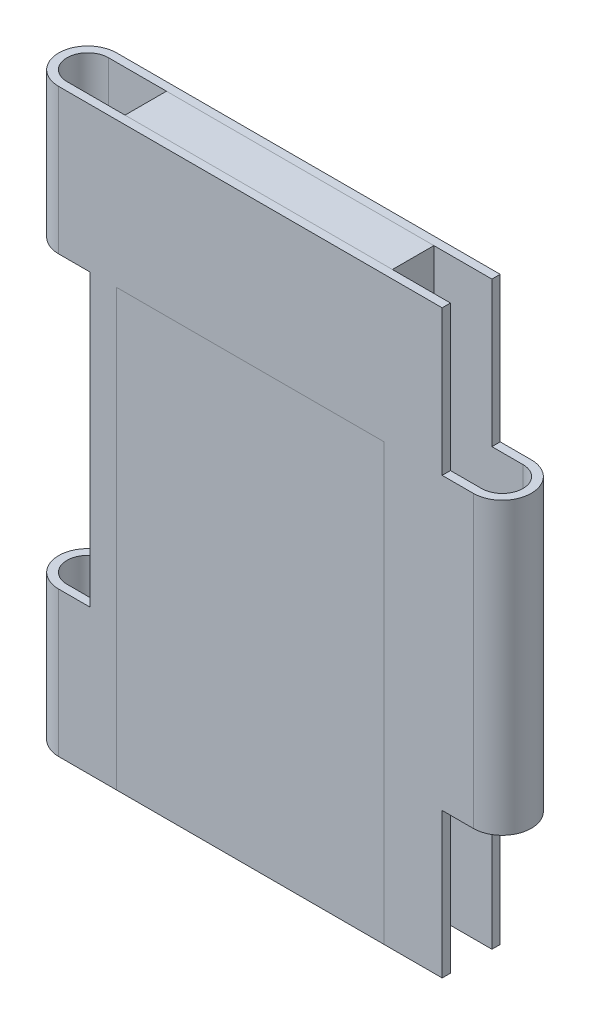
SolidWorks part; units mm, degrees
other "COLL.BOX-Boss-Extrude2"
ref_plane "Front Plane" through (0, 0, 0) normal (0, 0, 1) x (1, 0, 0)
ref_plane "Top Plane" through (0, 0, 0) normal (0, 1, 0) x (1, 0, 0)
ref_plane "Right Plane" through (0, 0, 0) normal (1, 0, 0) x (0, 0, -1)
sketch "Sketch1" plane through (0, 0, 0) normal (0, 1, 0) x (1, 0, 0)
  line L0 (-25, 0) -> (25, 0) construction
  line L1 (-25, 3.5) -> (25, 3.5)
  line L2 (-25, -3.5) -> (25, -3.5)
  line L3 (-25, 2.5) -> (25, 2.5)
  line L4 (-25, -2.5) -> (25, -2.5)
  arc A0 (-25, 3.5) -> (-25, -3.5) centre (-25, 0) ccw
  arc A1 (25, -3.5) -> (25, 3.5) centre (25, 0) ccw
  arc A2 (25, -2.5) -> (25, 2.5) centre (25, 0) ccw
  arc A3 (-25, 2.5) -> (-25, -2.5) centre (-25, 0) ccw
  point P2 (0, 0)
  dimension "D1" = 3.5
  dimension "50" = 50
  dimension "D2" = 1
extrude "Boss-Extrude1" add sketch "Sketch1" along normal blind 70
sketch "Sketch2" plane through (0, 0, 3.5) normal (0, 0, 1) x (1, 0, 0)
  line L5 (25, 70) -> (25, 0) construction
  line L6 (21.25, 52.5) -> (28.75, 52.5)
  line L7 (-25, 70) -> (-25, 0) construction
  line L8 (-28.75, 17.5) -> (-21.25, 17.5)
  line L9 (-28.75, 17.5) -> (-28.75, 52.5)
  line L10 (-28.75, 52.5) -> (-21.25, 52.5)
  line L11 (-21.25, 17.5) -> (-21.25, 52.5)
  line L12 (-28.75, 17.5) -> (-21.25, 52.5) construction
  line L13 (-28.75, 52.5) -> (-21.25, 17.5) construction
  line L15 (21.25, 52.5) -> (21.25, 70)
  line L16 (21.25, 70) -> (28.75, 70)
  line L17 (28.75, 52.5) -> (28.75, 70)
  line L20 (-25, 0) -> (25, 0) construction
  line L21 (21.25, 17.5) -> (28.75, 17.5)
  line L22 (21.25, 17.5) -> (21.25, 0)
  line L23 (21.25, 0) -> (28.75, 0)
  line L24 (28.75, 17.5) -> (28.75, 0)
  line L25 (21.25, 17.5) -> (28.75, 0) construction
  line L26 (21.25, 0) -> (28.75, 17.5) construction
  point P0 (25, 78.75)
  point P7 (-25, 35)
  point P14 (25, 8.75)
  dimension "D1" = 35
  dimension "D2" = 35
  dimension "D3" = 7.5
  dimension "D4" = 35
  dimension "D5" = 70
  dimension "D6" = 17.5
  dimension "D7" = 7.5
  dimension "D8" = 7.5
  dimension "D9" = 17.5
  dimension "D10" = 17.5
extrude "Cut-Extrude1" cut sketch "Sketch2" against normal up to surface (7 mm away) up to face at (0, 35, -3.5)
sketch "Sketch3" plane through (0, 70, 0) normal (0, 1, 0) x (1, 0, 0)
  line L0 (21.25, 3.5) -> (-25, 3.5) construction
  line L1 (-18, 3.5) -> (14.25, 3.5)
  line L2 (-18, 3.5) -> (-18, -3.5)
  line L3 (-18, -3.5) -> (14.25, -3.5)
  line L4 (14.25, 3.5) -> (14.25, -3.5)
  line L5 (-25, -3.5) -> (21.25, -3.5) construction
  line L6 (21.25, 3.5) -> (21.25, 2.5) construction
  arc A0 (-25, 3.5) -> (-25, -3.5) centre (-25, 0) ccw construction
  dimension "D1" = 7
  dimension "D2" = 7
extrude "Boss-Extrude2" add sketch "Sketch3" against normal up to vertex (70 mm away) separate body
